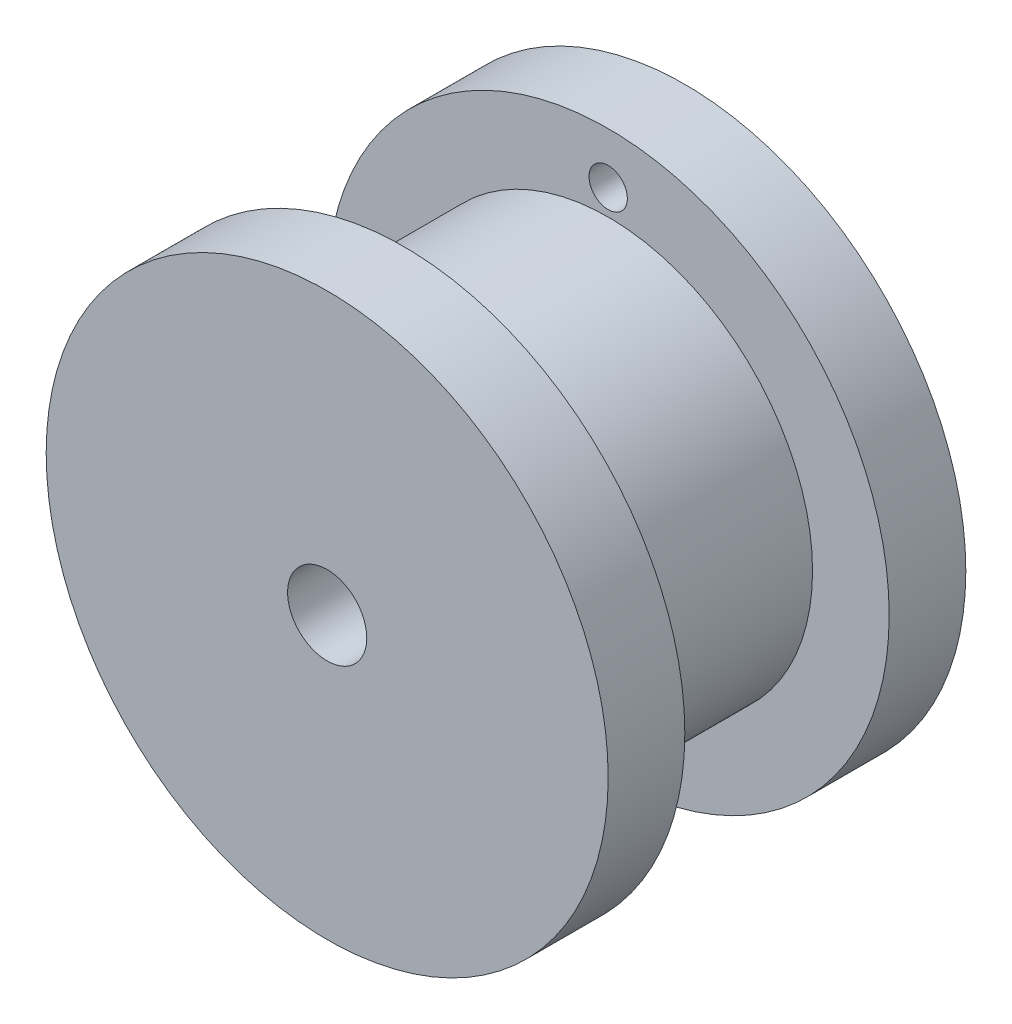
SolidWorks part; units mm, degrees
ref_plane "Front Plane" through (0, 0, 0) normal (0, 0, 1) x (1, 0, 0)
ref_plane "Top Plane" through (0, 0, 0) normal (0, 1, 0) x (1, 0, 0)
ref_plane "Right Plane" through (0, 0, 0) normal (1, 0, 0) x (0, 0, -1)
sketch "Sketch1" plane through (0, 0, 0) normal (0, 0, 1) x (1, 0, 0)
  circle A0 centre (0, 0) radius 11
  dimension "D1" = 22
extrude "Boss-Extrude1" add sketch "Sketch1" along normal blind 3
sketch "Sketch2" plane through (0, 0, 3) normal (0, 0, 1) x (1, 0, 0)
  circle A0 centre (0, 0) radius 8
  dimension "D1" = 16
extrude "Boss-Extrude2" add sketch "Sketch2" along normal blind 8
sketch "Sketch3" plane through (0, 0, 11) normal (0, 0, 1) x (1, 0, 0)
  circle A0 centre (0, 0) radius 11
  dimension "D1" = 22
extrude "Boss-Extrude3" add sketch "Sketch3" along normal blind 3
sketch "Sketch4" plane through (0, 0, 14) normal (0, 0, 1) x (1, 0, 0)
  circle A0 centre (0, 0) radius 1.55
  dimension "D1" = 3.1
extrude "Cut-Extrude1" cut sketch "Sketch4" against normal through all
sketch "Sketch5" plane through (0, 0, 3) normal (0, 0, 1) x (1, 0, 0)
  circle A0 centre (0, 9) radius 0.75
  point P2 (0, 0)
  dimension "D1" = 1.5
  dimension "D2" = 9
extrude "Cut-Extrude2" cut sketch "Sketch5" against normal through all
